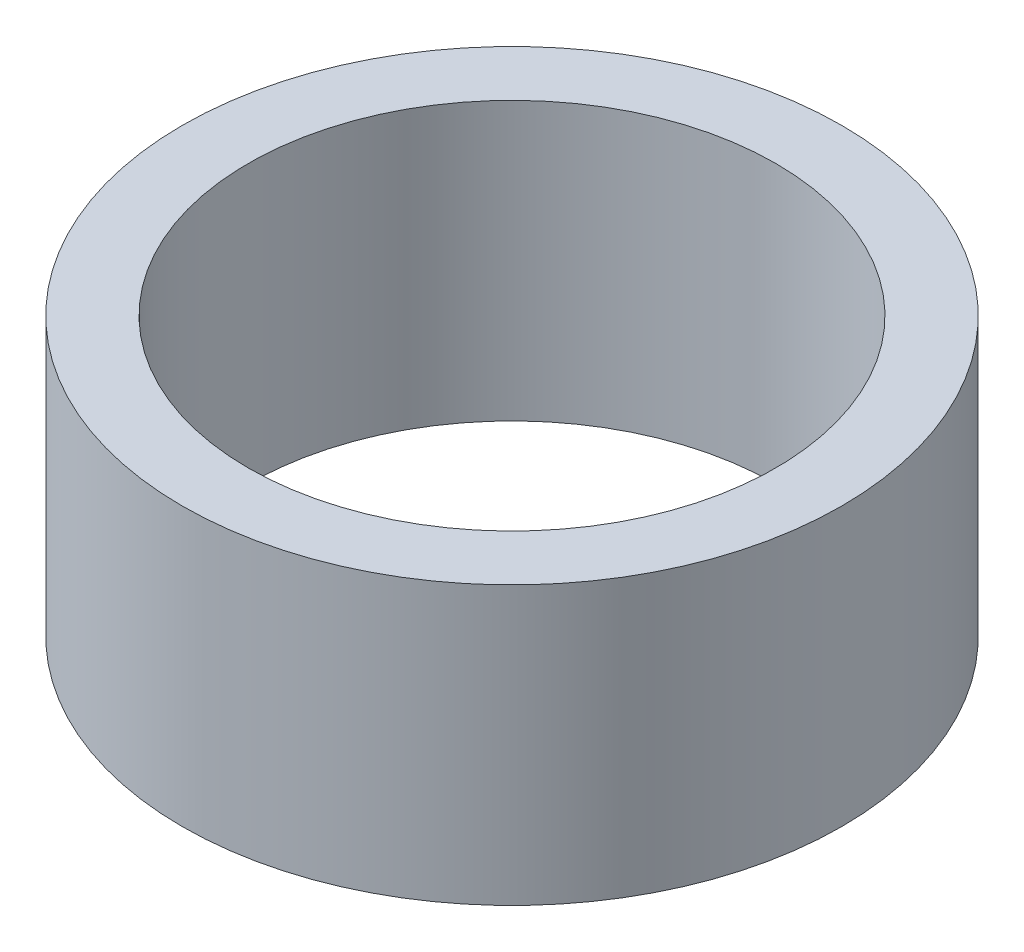
SolidWorks part; units mm, degrees
ref_plane "Front" through (0, 0, 0) normal (0, 0, 1) x (1, 0, 0)
ref_plane "Top" through (0, 0, 0) normal (0, 1, 0) x (1, 0, 0)
ref_plane "Right" through (0, 0, 0) normal (1, 0, 0) x (0, 0, -1)
sketch "Sketch1" plane through (0, 0, 0) normal (0, 1, 0) x (1, 0, 0)
  circle A0 centre (0, 0) radius 30.1625
  circle A1 centre (0, 0) radius 24.13
  dimension "D1" = 48.26
  dimension "D2" = 60.325
extrude "Boss-Extrude1" add sketch "Sketch1" along normal blind 25.4
